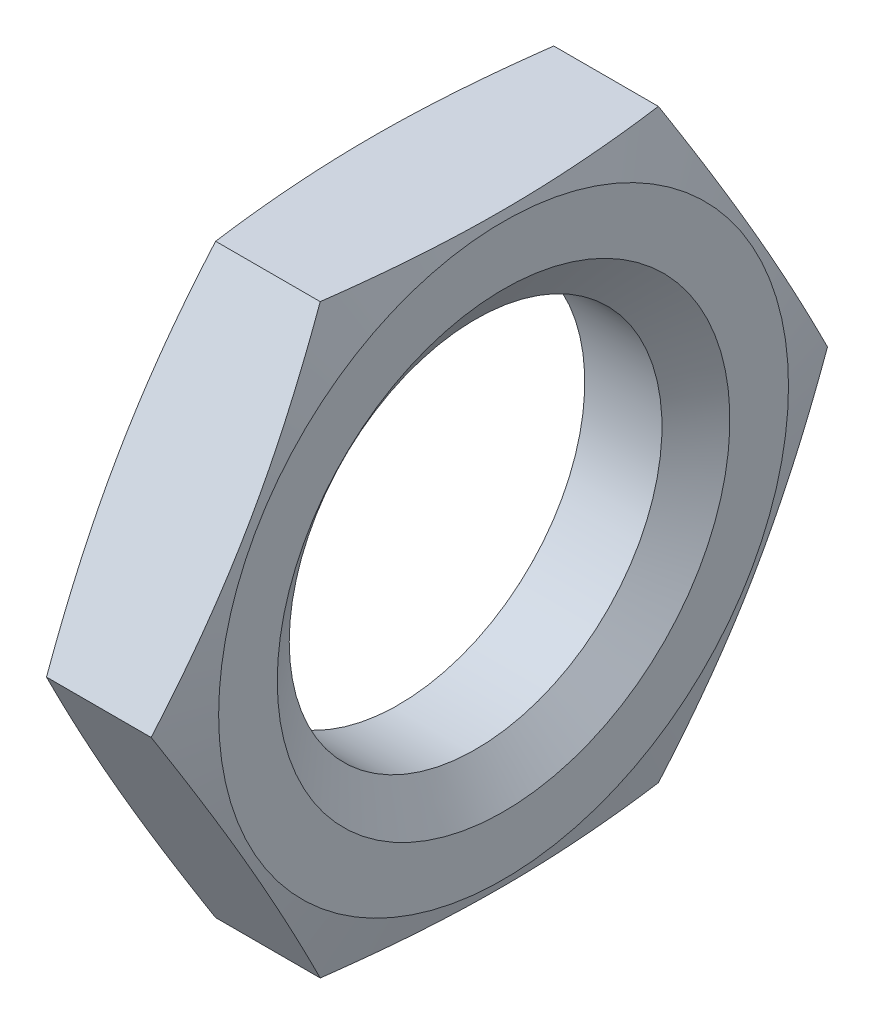
SolidWorks part; units mm, degrees
ref_plane "Спереди" through (0, 0, 0) normal (0, 0, 1) x (1, 0, 0)
ref_plane "Сверху" through (0, 0, 0) normal (0, 1, 0) x (1, 0, 0)
ref_plane "Справа" through (0, 0, 0) normal (1, 0, 0) x (0, 0, -1)
sketch "Эскиз1" plane through (0, 0, 0) normal (1, 0, 0) x (0, 0, -1)
  line L1 (6.3509, 0) -> (3.1754, 5.5)
  line L2 (3.1754, 5.5) -> (-3.1754, 5.5)
  line L3 (-3.1754, 5.5) -> (-6.3509, 0)
  line L4 (-6.3509, 0) -> (-3.1754, -5.5)
  line L5 (-3.1754, -5.5) -> (3.1754, -5.5)
  line L6 (3.1754, -5.5) -> (6.3509, 0)
  circle A0 centre (0, 0) radius 5.5 construction
  dimension "D1" = 11
extrude "Бобышка-Вытянуть1" add sketch "Эскиз1" along normal blind 2.5
sketch "Эскиз2" plane through (0, 0, 0) normal (0, 1, 0) x (1, 0, 0)
  line L0 (0, 5.3509) -> (0.2679, 6.3509)
  line L1 (0, 6.3509) -> (0, 3.1754) construction
  line L2 (2.5, 6.3509) -> (0, 6.3509) construction
  line L3 (0.2679, 6.3509) -> (2.2321, 6.3509)
  line L4 (2.2321, 6.3509) -> (2.5, 5.3509)
  line L5 (2.5, 6.3509) -> (2.5, 3.1754) construction
  line L6 (0, 0) -> (2.5, 0) construction
  line L7 (2.5, 3.1754) -> (2.5, -3.1754) construction
  line L8 (2.5, 5.3509) -> (4.5771, 5.3509)
  line L9 (4.5771, 5.3509) -> (4.5771, 7.7991)
  line L10 (4.5771, 7.7991) -> (-1.908, 7.7991)
  line L11 (-1.908, 7.7991) -> (-1.908, 5.3509)
  line L12 (-1.908, 5.3509) -> (0, 5.3509)
  dimension "D1" = 15
  dimension "D2" = 1
revolve "Вырез-Повернуть1" cut sketch "Эскиз2" angle 360 about L6
hole_wizard "Отверстие обработанное метчиком M8x1.01" positions "Эскиз4" profile "Эскиз3" tap size "M8x1.0" standard "Ansi (метрические)" end condition through all
sketch "Эскиз4" plane through (0, 0, 0) normal (-1, 0, 0) x (0, 0, 1)
  point P0 (0, 0)
sketch "Эскиз3" plane through (0, 0, 0) normal (0, 1, 0) x (0, 0, 1)
  line L0 (0, 0) -> (0, 2.5)
  line L1 (0, 2.5) -> (4.25, 2.5)
  line L2 (3.5, 1.9748) -> (3.5, 0.5252)
  line L3 (3.5, 0.5252) -> (4.25, 0)
  line L5 (4.25, 0) -> (0, 0)
  line L6 (-3.5, 0.5252) -> (-4.25, 0) construction
  line L7 (4.25, 2.5) -> (3.5, 1.9748)
  line L8 (-4.25, 2.5) -> (-3.5, 1.9748) construction
  line L11 (0, -6.35) -> (0, 107.95) construction
  dimension "Диаметр проходного сверла" = 7
  dimension "Глубина проходного сверла" = 2.5
  dimension "Диаметр передней зенковки" = 8.5
  dimension "Угол передней зенковки" = 110
  dimension "Диаметр задней зенковки" = 8.5
  dimension "Угол задней зенковки" = 110
cosmetic thread "Отверстие резьбы1" parameters "D2"=8
